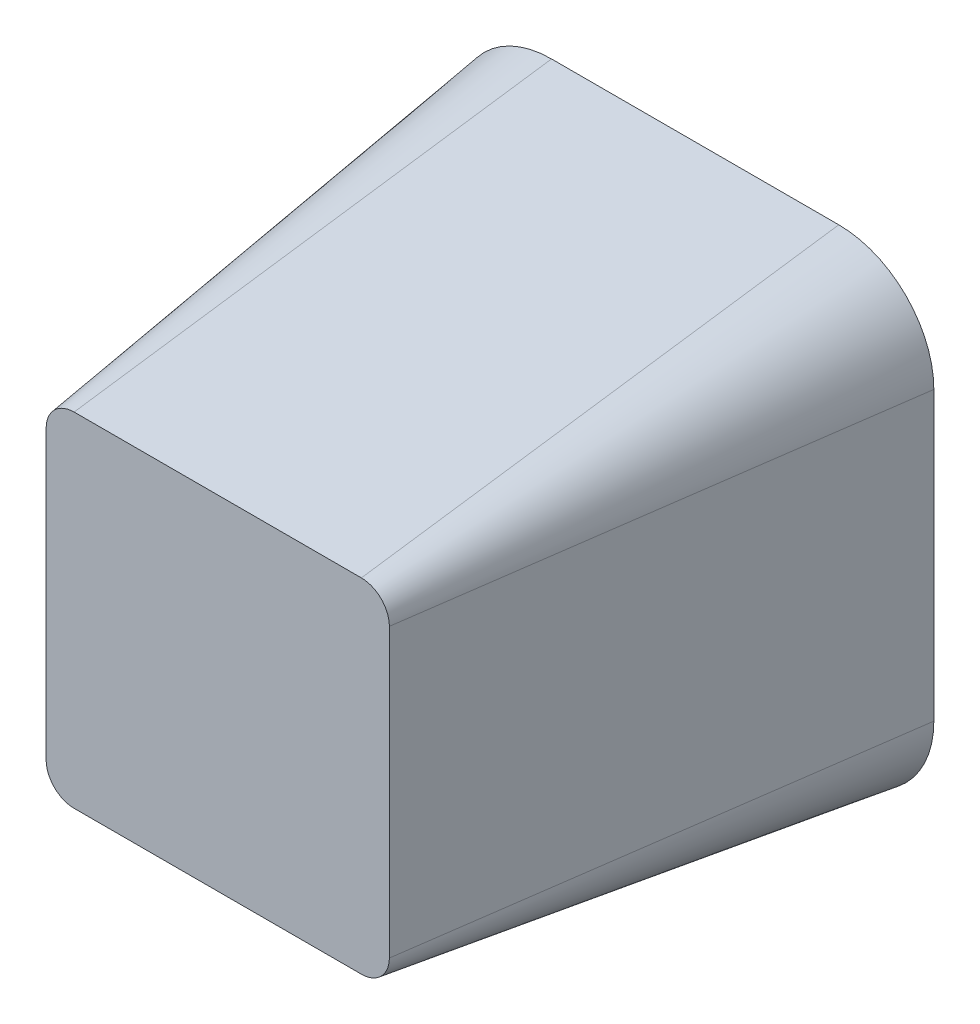
SolidWorks part; units mm, degrees
ref_plane "Front Plane" through (0, 0, 0) normal (0, 0, 1) x (1, 0, 0)
ref_plane "Top Plane" through (0, 0, 0) normal (0, 1, 0) x (1, 0, 0)
ref_plane "Right Plane" through (0, 0, 0) normal (1, 0, 0) x (0, 0, -1)
sketch "Sketch1" plane through (0, 0, 0) normal (0, 0, 1) x (1, 0, 0)
  line L1 (-6.8974, 3.8889) -> (-0.8803, 3.8889)
  line L2 (-8.8889, 1.8974) -> (-8.8889, -4.1197)
  line L3 (-6.8974, -6.1111) -> (-0.8803, -6.1111)
  line L4 (1.1111, 1.8974) -> (1.1111, -4.1197)
  line L5 (-4.3974, 1.4197) -> (-3.3803, 1.4197)
  line L6 (-6.3889, -0.5718) -> (-6.3889, -1.5889)
  line L7 (-4.3974, -3.5803) -> (-3.3803, -3.5803)
  line L8 (-1.3889, -0.5718) -> (-1.3889, -1.5889)
  arc A0 (-6.8974, 3.8889) -> (-8.8889, 1.8974) centre (-6.8974, 1.8974) ccw
  arc A1 (-6.8974, -6.1111) -> (-8.8889, -4.1197) centre (-6.8974, -4.1197) cw
  arc A2 (1.1111, -4.1197) -> (-0.8803, -6.1111) centre (-0.8803, -4.1197) cw
  arc A3 (1.1111, 1.8974) -> (-0.8803, 3.8889) centre (-0.8803, 1.8974) ccw
  arc A4 (-4.3974, 1.4197) -> (-6.3889, -0.5718) centre (-4.3974, -0.5718) ccw
  arc A5 (-3.3803, 1.4197) -> (-1.3889, -0.5718) centre (-3.3803, -0.5718) cw
  arc A6 (-3.3803, -3.5803) -> (-1.3889, -1.5889) centre (-3.3803, -1.5889) ccw
  arc A7 (-4.3974, -3.5803) -> (-6.3889, -1.5889) centre (-4.3974, -1.5889) cw
  point P6 (-8.8889, 3.8889)
  point P9 (-8.8889, -6.1111)
  point P14 (1.1111, 3.8889)
  point P21 (-6.3889, 1.4197)
  point P26 (-1.3889, -3.5803)
  point P29 (-6.3889, -3.5803)
  dimension "D3" = 1.9914
  dimension "D7" = 1.9914
  dimension "D1" = 10
  dimension "D2" = 10
  dimension "D4" = 5
  dimension "D5" = 5
  dimension "D6" = 2.5
extrude "Boss-Extrude1" add sketch "Sketch1" along normal blind 10 draft 8 contours A7 L7 A6 L8 A5 L5 A4 L6 | L4 A3 L1 A0 L2 A1 L3 A2 L7 A7 L6 A4 L5 A5 L8 A6
